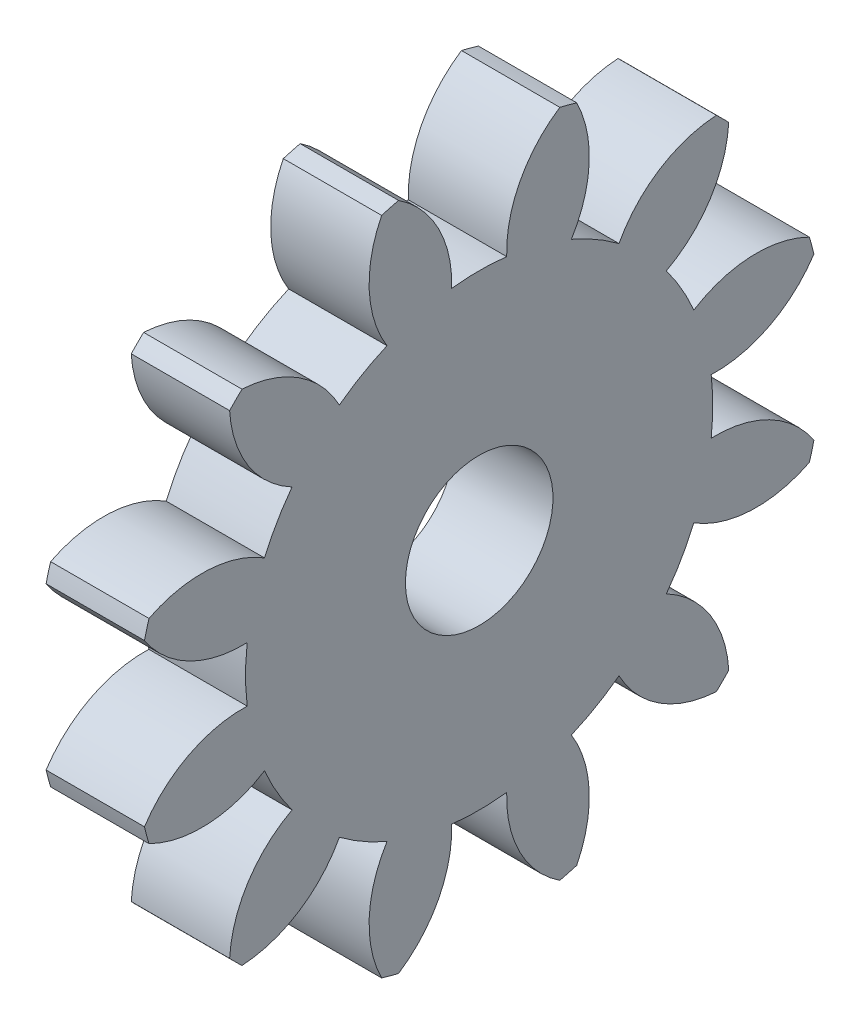
SolidWorks part; units mm, degrees
ref_plane "Plane1" through (0, 0, 0) normal (0, 0, 1) x (1, 0, 0)
ref_plane "Plane2" through (0, 0, 0) normal (0, 1, 0) x (1, 0, 0)
ref_plane "Plane3" through (0, 0, 0) normal (1, 0, 0) x (0, 0, -1)
other "Configuration Table"
sketch "HoldingSke" plane through (0, 0, 0) normal (0, 1, 0) x (1, 0, 0)
  line L0 (0, 0) -> (0.1534, -0.0354)
  line L1 (-15, 0) -> (100, 0) construction
  line L2 (0, 0) -> (-2.1039, 2.3779)
  line L3 (0, 0) -> (-11.863, 4.5341)
  line L4 (0, 0) -> (8.4473, 1.7955)
  line L5 (0, 0) -> (-23.7986, -8.8762)
  line L6 (0, 0) -> (-10.5278, -7.1032)
  line L7 (-2.1039, 2.3779) -> (3.3635, 27.1825)
  line L8 (-76.2, 54.61) -> (-73.66, 54.61)
  line L9 (-71.009, 38.7566) -> (-53.1078, 45.2721)
  line L10 (-76.2, 71.12) -> (104.1128, 71.12)
  line L11 (0, 0) -> (-12.7, 0)
  line L12 (-76.2, 101.6) -> (-75.9714, 101.6)
  line L13 (24.9733, 27.94) -> (52.9518, 28.4284)
  line L14 (24.9733, 27.94) -> (24.9746, 27.94)
  line L15 (24.9733, 27.94) -> (100.4006, 29.5858)
  line L16 (-63.627, -6.35) -> (-12.827, -6.35)
  circle A0 centre (0, 0) radius 9.525
  circle A1 centre (0, 0) radius 12.7
  circle A2 centre (0, 0) radius 12.7
  circle A3 centre (0, 0) radius 9.525
  dimension "Ap" = 20
  dimension "H" = 19.05
  dimension "Pitch_radius" = 180.3128
  dimension "Addendum_fac" = 1
  dimension "Dedendum_fac" = 1.25
  dimension "Clearance_fac" = 0.25
  dimension "Dedendum_add" = 0.0013
sketch "BasProSke" plane through (0, 0, 0) normal (0, 1, 0) x (1, 0, 0)
  line L0 (-10, 0) -> (60, 0) construction
  line L1 (0, 0) -> (0, 44.45)
  line L2 (0, 0) -> (12.7, 0)
  line L3 (12.7, 0) -> (12.7, 44.45)
  line L4 (12.7, 44.45) -> (0, 44.45)
revolve "Base-Revolve" add sketch "BasProSke" angle 360 about L0
sketch "TooCutSke" plane through (0, 0, 0) normal (1, 0, 0) x (0, 0, -1)
  line L1 (0, 0) -> (0, 107) construction
  line L2 (0, 0) -> (-5.3725, 37.7193) construction
  line L3 (0, 0) -> (-19.5794, 73.0714) construction
  line L4 (-5.3725, 37.7193) -> (-9.7897, 36.5357) construction
  arc A0 (3.5522, 29.9513) -> (-3.5522, 29.9513) centre (0, 0) ccw
  arc A1 (10.4397, 43.2328) -> (-10.4397, 43.2328) centre (0, 0) ccw
  circle A2 centre (0, 0) radius 38.1 construction
  circle A3 centre (0, 0) radius 35.8023 construction
  arc A4 (-3.5522, 29.9513) -> (-10.4397, 43.2328) centre (-18.7831, 30.4795) ccw
  arc A5 (10.4397, 43.2328) -> (3.5522, 29.9513) centre (18.7831, 30.4795) ccw
extrude "ToothCut" cut sketch "TooCutSke" along normal through all
fillet "Breaks" [suppressed] radius 0.127
fillet "RootFillets" [suppressed] radius 1.5888
pattern_circular "TeethCuts" count 12 every 30 about axis through (-10, 0, 0) along (1, 0, 0) of "ToothCut", "RootFillets", "Breaks"
sketch "HubNeaOneSke" plane through (0, 0, 0) normal (-1, 0, 0) x (0, 0, 1)
  circle A0 centre (0, 0) radius 12.7
extrude "HubNearOne" [suppressed] add sketch "HubNeaOneSke" along normal blind 12.7001
sketch "HubNeaBotSke" plane through (0, 0, 0) normal (-1, 0, 0) x (0, 0, 1)
  circle A0 centre (0, 0) radius 12.7
extrude "HubNearBoth" [suppressed] add sketch "HubNeaBotSke" along normal blind 6.35
ref_plane "FarPln" through (12.7, 0, 0) normal (1, 0, 0) x (0, 0, -1)
sketch "HubFarSke" plane through (12.7, 0, 0) normal (1, 0, 0) x (0, 0, -1)
  circle A0 centre (0, 0) radius 12.7
extrude "HubFar" [suppressed] add sketch "HubFarSke" along normal blind 6.35
sketch "BorSke" plane through (0, 0, 0) normal (1, 0, 0) x (0, 0, -1)
  circle A0 centre (0, 0) radius 9.525
extrude "Bore" cut sketch "BorSke" along normal mid plane 50.8001
sketch "KeySke" plane through (0, 0, 0) normal (1, 0, 0) x (0, 0, -1)
  line L0 (-3.175, 0) -> (-3.175, 12.065)
  line L1 (-3.175, 12.065) -> (3.175, 12.065)
  line L2 (3.175, 12.065) -> (3.175, 0)
  line L3 (0, 0) -> (0, 34) construction
  line L4 (-3.175, 0) -> (3.175, 0)
extrude "Keyway" [suppressed] cut sketch "KeySke" along normal mid plane 50.8001
pattern_circular "Keyway2" [suppressed] count 2 every 90 about axis through (-10, 0, 0) along (1, 0, 0)
equation "' \"Module@HoldingSke\" = 6.35"
equation "' \"Num_teeth@HoldingSke\" = 12"
equation "' \"Ap@HoldingSke\" =  20"
equation "' \"Ap@HoldingSke\" = 20"
equation "' \"Width@HoldingSke\" = 0.5 * 25.4"
equation "' \"Hub_dia@HoldingSke\"= 1 * 25.4"
equation "' \"Hub_dia@HoldingSke\" = 1 * 25.4"
equation "' \"Overall_len@HoldingSke\" = 1.0 * 25.4"
equation "' \"Bore@HoldingSke\" = 0.75 * 25.4"
equation "' \"T_dim@HoldingSke\" = 0.1 * 25.4"
equation "' \"Width@KeySke\" = 0.25 * 25.4"
equation "' \"Show_teeth@HoldingSke\" = 13"
equation "' \"Backlash@HoldingSke\" = 0.009 * 25.4"
equation "' \"Addendum_fac@HoldingSke\" = 1.0"
equation "' \"Dedendum_fac@HoldingSke\" = 1.25"
equation "' \"Dedendum_add@HoldingSke\" = 0.00005 * 25.4"
equation "' \"Clearance_fac@HoldingSke\" = 0.25"
equation "\"Pitch@HoldingSke\" = 1 / \"Module@HoldingSke\""
equation "\"Overcut_dia@TooCutSke\" = (\"Num_teeth@HoldingSke\" + 2 * \"Addendum_fac@HoldingSke\") / \"Pitch@HoldingSke\" + 0.002 * 25.4"
equation "\"Pitch_dia@TooCutSke\" = \"Num_teeth@HoldingSke\" / \"Pitch@HoldingSke\""
equation "\"Base_dia@TooCutSke\" = \"Num_teeth@HoldingSke\" / \"Pitch@HoldingSke\" * cos((\"Ap@HoldingSke\"  * 3.14159265 / 180))"
equation "\"Root_dia@TooCutSke\" = (\"Num_teeth@HoldingSke\" + 2) / \"Pitch@HoldingSke\" - 2 * (\"Addendum_fac@HoldingSke\" + \"Dedendum_fac@HoldingSke\") / \"Pitch@HoldingSke\" - \"Dedendum_add@HoldingSke\" * 2"
equation "\"Half_ang@TooCutSke\" = 180 / \"Num_teeth@HoldingSke\""
equation "\"Half_CT@TooCutSke\" = \"Num_teeth@HoldingSke\" / \"Pitch@HoldingSke\" * sin((3.14159265 / 2 / \"Num_teeth@HoldingSke\")) / 2 - 7 * \"Backlash@HoldingSke\" / 4"
equation "\"Flank_rad@TooCutSke\" = \"Num_teeth@HoldingSke\" / \"Pitch@HoldingSke\" / 5"
equation "\"Radius@RootFillets\" = \"Clearance_fac@HoldingSke\" / \"Pitch@HoldingSke\" + \"Dedendum_add@HoldingSke\""
equation "\"Break_rad@Breaks\" = 0.02 / \"Pitch@HoldingSke\""
equation "\"Thickness@HoldingSke\" = \"Width@HoldingSke\""
equation "\"OAL@HoldingSke\" = \"Thickness@HoldingSke\""
equation "\"MHD@HoldingSke\" = (\"Num_teeth@HoldingSke\" + 2) / \"Pitch@HoldingSke\" - 2 * (\"Addendum_fac@HoldingSke\" + \"Dedendum_fac@HoldingSke\")  / \"Pitch@HoldingSke\" - \"Dedendum_add@HoldingSke\" * 2"
equation "\"MBD@HoldingSke\" = (\"Num_teeth@HoldingSke\" + 2) / \"Pitch@HoldingSke\" - 2 * (\"Addendum_fac@HoldingSke\" + \"Dedendum_fac@HoldingSke\")  / \"Pitch@HoldingSke\" - \"Dedendum_add@HoldingSke\" * 2 - 0.002 * 25.4"
equation "\"MHD@HoldingSke\" = ((sgn( \"MHD@HoldingSke\" - \"Hub_dia@HoldingSke\" )-1)*( \"MHD@HoldingSke\" - \"Hub_dia@HoldingSke\" ))/-2+ \"Hub_dia@HoldingSke\""
equation "\"MBD@HoldingSke\" = ((sgn( \"MBD@HoldingSke\" - \"Bore@HoldingSke\" )-1)*( \"MBD@HoldingSke\" - \"Bore@HoldingSke\" ))/-2+ \"Bore@HoldingSke\""
equation "\"OAL@HoldingSke\" = ((sgn( \"OAL@HoldingSke\" - \"Overall_len@HoldingSke\" )+1)*( \"OAL@HoldingSke\" - \"Overall_len@HoldingSke\" ))/2 + \"Overall_len@HoldingSke\" + 0.000002 * 25.4"
equation "\"Num_teeth@TeethCuts\" = int( \"Show_teeth@HoldingSke\" ) + 1"
equation "\"Num_teeth@TeethCuts\" = ((sgn( \"Num_teeth@TeethCuts\" - \"Num_teeth@HoldingSke\" )-1)*( \"Num_teeth@TeethCuts\" - \"Num_teeth@HoldingSke\" ))/-2+ \"Num_teeth@HoldingSke\""
equation "\"Num_teeth@TeethCuts\" = ((sgn( \"Num_teeth@TeethCuts\" - 2.0)+1)*( \"Num_teeth@TeethCuts\" - 2.0))/2 +2.0"
equation "\"Angle@TeethCuts\" = 360.0 / \"Num_teeth@HoldingSke\""
equation "\"Diameter@BasProSke\" = (\"Num_teeth@HoldingSke\" + 2 * \"Addendum_fac@HoldingSke\") / \"Pitch@HoldingSke\""
equation "\"Thickness@BasProSke\"  = \"Thickness@HoldingSke\""
equation "' \"Fillet_rad@BasProSke\" =  \"Thickness@HoldingSke\" * 0.05"
equation "' \"Fillet_rad@BasProSke\" = \"Thickness@HoldingSke\" * 0.05"
equation "\"MHD@HoldingSke\" = ((sgn( \"MHD@HoldingSke\" - \"Root_dia@TooCutSke\" )-1)*( \"MHD@HoldingSke\" - \"Root_dia@TooCutSke\" ))/-2+ \"Root_dia@TooCutSke\""
equation "\"Diameter@HubNeaOneSke\" = \"MHD@HoldingSke\""
equation "\"Length@HubNearOne\" = \"OAL@HoldingSke\" - \"Thickness@BasProSke\""
equation "\"Diameter@HubNeaBotSke\" = \"MHD@HoldingSke\""
equation "\"Length@HubNearBoth\" = ( \"OAL@HoldingSke\" - \"Thickness@BasProSke\" ) / 2.0"
equation "\"Thickness@FarPln\" = \"Thickness@BasProSke\""
equation "\"Diameter@HubFarSke\" = \"MHD@HoldingSke\""
equation "\"Length@HubFar\" = ( \"OAL@HoldingSke\" - \"Thickness@BasProSke\" ) / 2.0"
equation "\"Diameter@BorSke\" = \"MBD@HoldingSke\""
equation "\"D1@Bore\" = \"OAL@HoldingSke\" * 2.0"
equation "\"D1@Keyway\" = \"OAL@HoldingSke\" * 2.0"
equation "\"Offset@KeySke\" = \"T_dim@HoldingSke\" + \"MBD@HoldingSke\" / 2.0"
